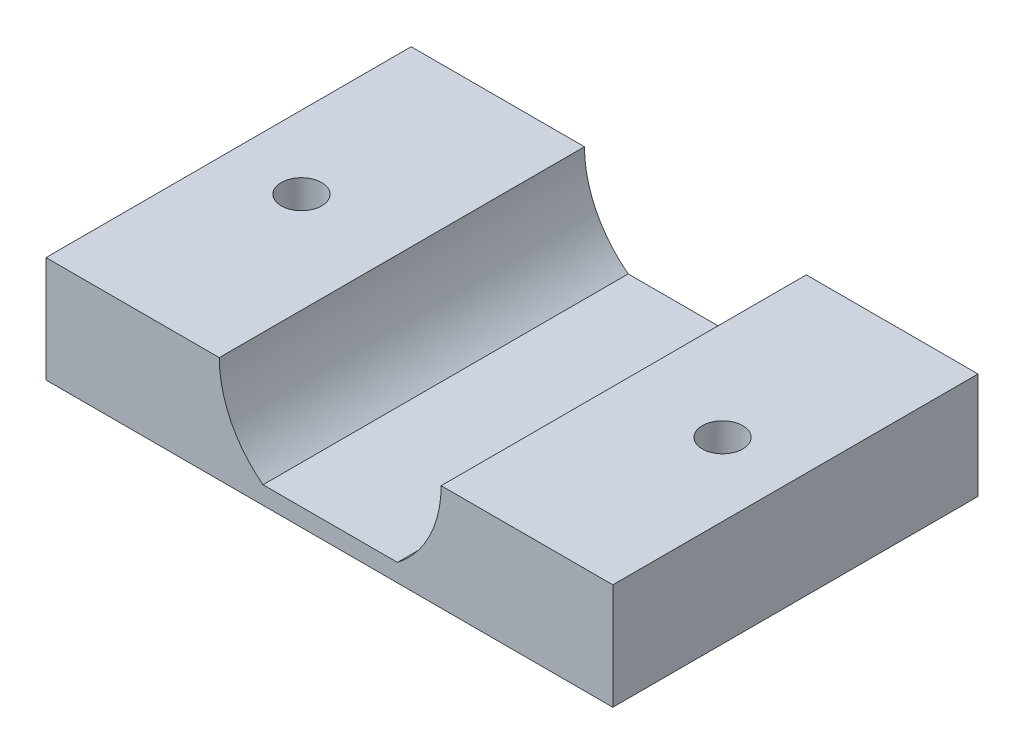
SolidWorks part; units mm, degrees
ref_plane "Front" through (0, 0, 0) normal (0, 0, 1) x (1, 0, 0)
ref_plane "Top" through (0, 0, 0) normal (0, 1, 0) x (1, 0, 0)
ref_plane "Right" through (0, 0, 0) normal (1, 0, 0) x (0, 0, -1)
sketch "Sketch1" plane through (0, 0, 0) normal (0, 0, 1) x (1, 0, 0)
  line L1 (-49.45, 62.225) -> (49.45, 62.225)
  line L2 (-49.45, 62.225) -> (-49.45, -62.225)
  line L3 (-49.45, -62.225) -> (49.45, -62.225)
  line L4 (49.45, 62.225) -> (49.45, -62.225)
  line L5 (-49.45, 62.225) -> (49.45, -62.225) construction
  line L6 (-49.45, -62.225) -> (49.45, 62.225) construction
  point P0 (0, 0)
  dimension "D1" = 124.45
  dimension "D2" = 98.9
extrude "body" add sketch "Sketch1" along normal blind 22.55
sketch "Sketch4" plane through (0, 0, 0) normal (0, 0, -1) x (-1, 0, 0)
  line L0 (-49.45, 62.225) -> (49.45, 62.225) construction
  line L1 (3.5, 60.725) -> (-3.5, 60.725)
  line L2 (3.5, 60.725) -> (3.5, 63.725)
  line L3 (3.5, 63.725) -> (-3.5, 63.725)
  line L4 (-3.5, 60.725) -> (-3.5, 63.725)
  line L5 (3.5, 60.725) -> (-3.5, 63.725) construction
  line L6 (3.5, 63.725) -> (-3.5, 60.725) construction
  line L19 (47.85, 9.275) -> (50.85, 9.275)
  line L20 (47.85, 9.275) -> (47.85, 16.275)
  line L21 (47.85, 16.275) -> (50.85, 16.275)
  line L22 (50.85, 9.275) -> (50.85, 16.275)
  line L23 (-3.6, -35.075) -> (-3.6, -38.075)
  line L24 (-3.6, -35.075) -> (3.4, -35.075)
  line L25 (3.4, -35.075) -> (3.4, -38.075)
  line L26 (-3.6, -38.075) -> (3.4, -38.075)
  line L27 (-47.95, 16.375) -> (-50.95, 16.375)
  line L28 (49.45, 62.225) -> (49.45, -62.225) construction
  line L29 (-47.95, 16.375) -> (-47.95, 9.375)
  line L30 (-47.95, 9.375) -> (-50.95, 9.375)
  line L31 (-50.95, 16.375) -> (-50.95, 9.375)
  circle A0 centre (0, 12.875) radius 27.5
  point P0 (0, 62.225)
  point P9 (49.35, 16.275)
  dimension "D5" = 55
  dimension "D6" = 49.45
  dimension "D1" = 7
  dimension "D2" = 3
  dimension "D4" = 47.85
  dimension "D7" = 47.85
  dimension "D8" = 45.95
  dimension "D3" = 4
extrude "Cut-Extrude1" cut sketch "Sketch4" against normal blind 63 contours L1 L4 L3 L2 | L22 L21 L20 L19 | L29 L30 L31 L27
sketch "Sketch5" plane through (0, 0, 0) normal (0, 0, -1) x (-1, 0, 0)
  line L0 (-47.95, 12.875) -> (47.85, 12.775) construction
  line L1 (-47.95, 16.375) -> (-47.95, 9.375) construction
  line L2 (47.85, 9.275) -> (47.85, 16.275) construction
  line L3 (47.85, 12.775) -> (0, 60.725) construction
  line L4 (3.5, 60.725) -> (-3.5, 60.725) construction
  line L6 (-0.05, 12.825) -> (0, 60.725) construction
  line L8 (-4.1997, 7.375) -> (4.0997, 7.375)
  line L9 (-4.1997, 7.375) -> (-4.1997, 18.275)
  line L10 (-4.1997, 18.275) -> (4.0997, 18.275)
  line L11 (4.0997, 7.375) -> (4.0997, 18.275)
  line L12 (-4.1997, 7.375) -> (4.0997, 18.275) construction
  line L13 (-4.1997, 18.275) -> (4.0997, 7.375) construction
  circle A0 centre (-0.05, 12.825) radius 6.85
  dimension "D1" = 13.7
  dimension "D2" = 5.45
extrude "Cut-Extrude2" cut sketch "Sketch5" against normal blind 63 contours L8 L11 L10 L9 | L11 A0 | L9 A0
sketch "Sketch6" plane through (0, 0, 0) normal (0, 0, -1) x (-1, 0, 0)
  line L0 (47.85, 16.275) -> (49.45, 16.275) construction
  line L1 (49.45, 62.225) -> (6.5, 62.225)
  line L2 (49.45, 62.225) -> (49.45, 19.275)
  line L3 (49.45, 19.275) -> (6.5, 19.275)
  line L4 (6.5, 62.225) -> (6.5, 19.275)
  line L5 (3.5, 60.725) -> (3.5, 62.225) construction
  line L6 (3.5, 60.725) -> (-3.5, 60.725) construction
  line L8 (0, 60.725) -> (-0.05, 18.275) construction
  line L9 (-4.1997, 18.275) -> (4.0997, 18.275) construction
  line L10 (-49.5475, 19.3916) -> (-6.5976, 19.2904)
  line L11 (-6.4964, 62.2403) -> (-6.5976, 19.2904)
  line L12 (-49.4463, 62.3415) -> (-6.4964, 62.2403)
  line L13 (-49.4463, 62.3415) -> (-49.5475, 19.3916)
  line L14 (49.45, 9.275) -> (49.45, -62.225) construction
  line L15 (-49.45, -62.225) -> (49.45, -62.225)
  line L16 (-49.45, -62.225) -> (-49.45, 6.275)
  line L17 (-49.45, 6.275) -> (49.45, 6.275)
  line L18 (49.45, -62.225) -> (49.45, 6.275)
  line L19 (47.85, 9.275) -> (49.45, 9.275) construction
  circle A0 centre (6.5, 19.275) radius 3
  circle A1 centre (-6.5976, 19.2904) radius 3
  point P7 (48.65, 16.275)
  line M15 (49.45, 62.225) -> (3.5, 62.225)
  line M19 (-3.5, 62.225) -> (-49.45, 62.225)
  line M20 (-49.45, 62.225) -> (-49.45, 16.375)
  line M24 (-49.45, 9.375) -> (-49.45, -62.225)
  line M25 (-49.45, -62.225) -> (49.45, -62.225)
  line M26 (49.45, -62.225) -> (49.45, 9.275)
  line M30 (49.45, 16.275) -> (49.45, 62.225)
  dimension "D3" = 6
  dimension "D1" = 3
  dimension "D2" = 3
  dimension "D4" = 3
extrude "Cut-Extrude3" cut sketch "Sketch6" against normal blind 63 contours A0 L3 L4 M30 M15 | L10 A1 L11 L13 M19 M20 | L17 M24 M25 M26
sketch "Sketch7" plane through (49.5929, 0.1168, 0) normal (-1, -0.0024, 0) x (0, 0, 1)
  line L1 (0, 62.1083) -> (22.55, 62.1083)
  line L2 (0, 62.1083) -> (0, 60.6666)
  line L3 (0, 60.6666) -> (22.55, 60.6666)
  line L4 (22.55, 62.1083) -> (22.55, 60.6666)
extrude "Cut-Extrude4" cut sketch "Sketch7" against normal blind 63
sketch "Sketch8" plane through (0, 0, 22.55) normal (0, 0, 1) x (1, 0, 0)
  line L0 (-49.45, 6.275) -> (49.45, 6.275) construction
  line L1 (-17.5, -0.275) -> (17.5, -0.275)
  line L2 (-17.5, -0.275) -> (-17.5, 12.825)
  line L3 (-17.5, 12.825) -> (17.5, 12.825)
  line L4 (17.5, -0.275) -> (17.5, 12.825)
  line L5 (-17.5, -0.275) -> (17.5, 12.825) construction
  line L6 (-17.5, 12.825) -> (17.5, -0.275) construction
  line L7 (6.9, 12.825) -> (-6.8, 12.825) construction
  line L9 (49.45, 6.275) -> (-51.5947, 6.275)
  line L10 (49.45, 6.275) -> (49.45, 70.0262)
  line L11 (49.45, 70.0262) -> (-51.5947, 70.0262)
  line L12 (-51.5947, 6.275) -> (-51.5947, 70.0262)
  arc A0 (4.1997, 7.375) -> (4.1997, 18.275) centre (0.05, 12.825) ccw construction
  arc A1 (-4.0997, 18.275) -> (-4.0997, 7.375) centre (0.05, 12.825) ccw construction
  point P0 (0, 6.275)
  arc M10 (-4.0997, 7.375) -> (-4.0997, 18.275) centre (0.05, 12.825) cw
  line M11 (-4.0997, 18.275) -> (4.1997, 18.275)
  arc M12 (4.1997, 18.275) -> (4.1997, 7.375) centre (0.05, 12.825) cw
  line M13 (-49.45, 9.275) -> (-49.45, 6.275)
  line M14 (-49.45, 6.275) -> (49.45, 6.275)
  line M15 (49.45, 6.275) -> (49.45, 9.375)
  line M16 (49.45, 9.375) -> (47.95, 9.375)
  line M17 (47.95, 9.375) -> (47.95, 16.375)
  line M18 (47.95, 16.375) -> (49.45, 16.375)
  line M19 (49.45, 16.375) -> (49.45, 19.3914)
  line M20 (49.45, 19.3914) -> (9.5976, 19.2975)
  arc M21 (9.5976, 19.2975) -> (6.5906, 22.2904) centre (6.5976, 19.2904) ccw
  line M22 (6.5906, 22.2904) -> (6.4965, 62.225)
  line M23 (6.4965, 62.225) -> (3.5, 62.225)
  line M24 (3.5, 62.225) -> (3.5, 60.725)
  line M25 (3.5, 60.725) -> (-3.5, 60.725)
  line M26 (-3.5, 60.725) -> (-3.5, 62.225)
  line M27 (-3.5, 62.225) -> (-6.5, 62.225)
  line M28 (-6.5, 62.225) -> (-6.5, 22.275)
  arc M29 (-6.5, 22.275) -> (-9.5, 19.275) centre (-6.5, 19.275) ccw
  line M30 (-9.5, 19.275) -> (-49.45, 19.275)
  line M31 (-49.45, 19.275) -> (-49.45, 16.275)
  line M32 (-49.45, 16.275) -> (-47.85, 16.275)
  line M33 (-47.85, 16.275) -> (-47.85, 9.275)
  line M34 (-47.85, 9.275) -> (-49.45, 9.275)
  dimension "D1" = 0
  dimension "D2" = 35
  dimension "D3" = 63.7512
  dimension "D4" = 101.0447
extrude "Cut-Extrude5" cut sketch "Sketch8" against normal through all contours L4 L2 L3 M14 M15 M16 M17 M18 M19 M20 M21 M22 M23 M24 M25 M26 M27 M28 M29 M30 M31 M32 M33 M34 M13 M10 M11 M12
sketch "Sketch9" plane through (0, 6.275, 0) normal (0, -1, 0) x (1, 0, 0)
  line L0 (17.5, 11.275) -> (-17.5, 11.275) construction
  line L1 (17.5, 0) -> (17.5, 22.55) construction
  line L2 (-17.5, 0) -> (-17.5, 22.55) construction
  line L3 (0, 22.55) -> (0, 0) construction
  line L4 (-17.5, 22.55) -> (17.5, 22.55) construction
  line L5 (17.5, 0) -> (-17.5, 0) construction
  circle A0 centre (13, 11.275) radius 1.25
  circle A1 centre (-13, 11.275) radius 1.25
  dimension "D1" = 2.5
  dimension "D2" = 4.5
extrude "Cut-Extrude6" cut sketch "Sketch9" against normal blind 10
